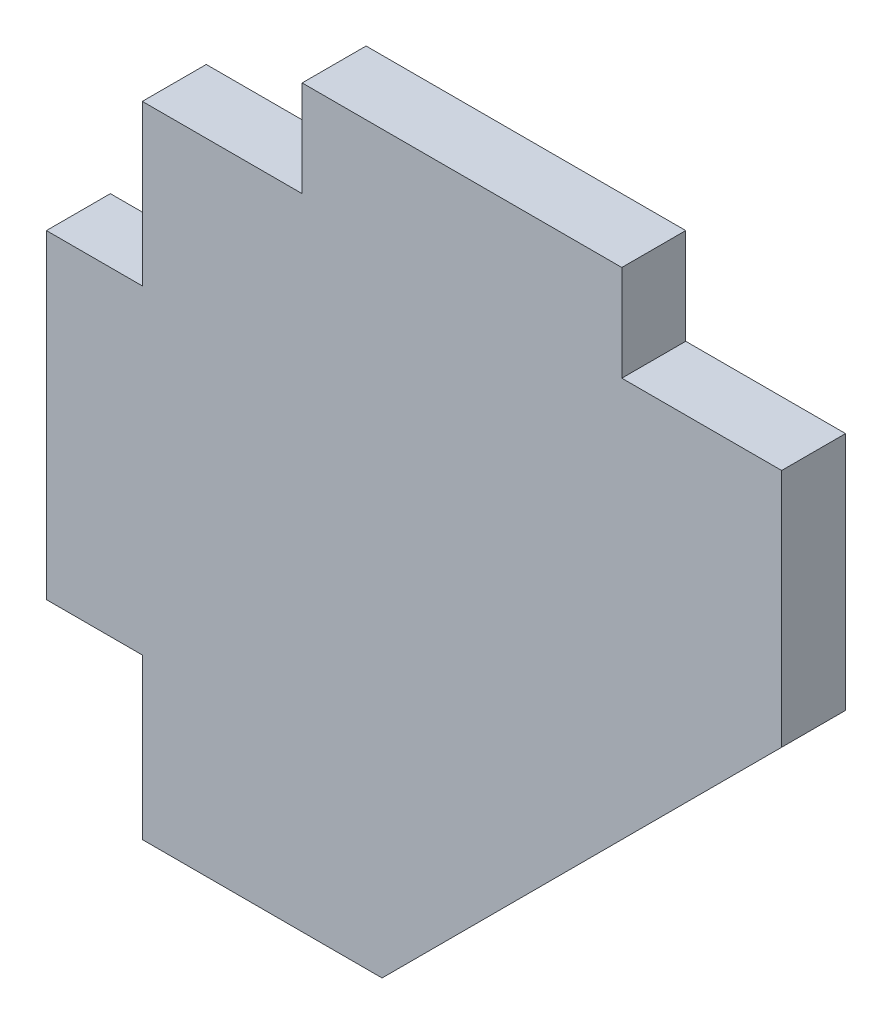
SolidWorks part; units mm, degrees
ref_plane "Face" through (0, 0, 0) normal (0, 0, 1) x (1, 0, 0)
ref_plane "Dessus" through (0, 0, 0) normal (0, 1, 0) x (1, 0, 0)
ref_plane "Droite" through (0, 0, 0) normal (1, 0, 0) x (0, 0, -1)
sketch "Esquisse1" plane through (0, 0, 0) normal (0, 0, 1) x (1, 0, 0)
  line L0 (-2459.7238, -34) -> (-2459.7238, -98) construction
  line L1 (-2459.7238, -14) -> (-2453.7238, -14)
  line L2 (-2459.7238, -14) -> (-2459.7238, -34)
  line L3 (-2459.7238, -34) -> (-2453.7238, -34)
  line L5 (-2453.7238, -34) -> (-2453.7238, -98) construction
  line L7 (-2423.7238, 2) -> (-2443.7238, 2)
  line L8 (-2423.7238, 2) -> (-2423.7238, -4)
  line L10 (-2443.7238, 2) -> (-2443.7238, -4)
  line L12 (-2453.7238, -34) -> (-2453.7238, -44)
  line L13 (-2413.7238, -4) -> (-2423.7238, -4)
  line L14 (-2413.7238, -4) -> (-2413.7238, -19)
  line L15 (-2438.7238, -44) -> (-2453.7238, -44)
  line L16 (-2453.7238, -4) -> (-2453.7238, -14)
  line L17 (-2443.7238, -4) -> (-2453.7238, -4)
  line L18 (-2413.7238, -19) -> (-2438.7238, -44)
  line L19 (-2443.7238, -4) -> (-2459.7238, -4) construction
  line L20 (-2443.7238, 2) -> (-2459.7238, 2) construction
  point P18 (-2413.7238, -44)
  dimension "D1" = 20
  dimension "D2" = 10
  dimension "D3" = 20
  dimension "D4" = 10
  dimension "D5" = 10
  dimension "D6" = 10
extrude "Boss.-Extru.1" add sketch "Esquisse1" against normal blind 4
